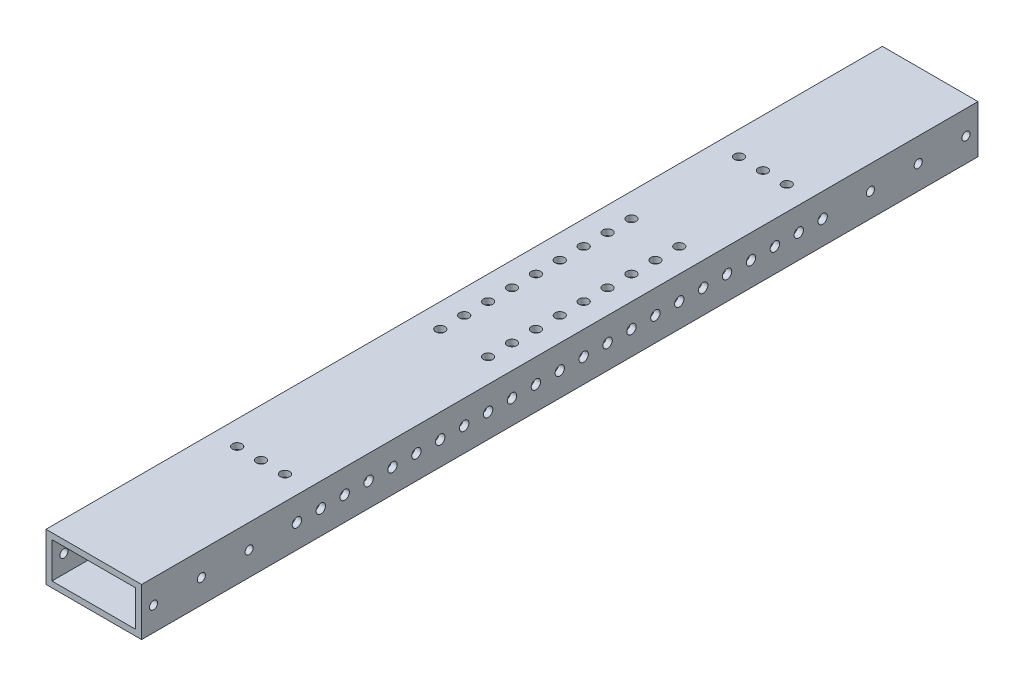
SolidWorks part; units mm, degrees
material "6061-T6 (SS)"
ref_plane "Front Plane" through (0, 0, 0) normal (0, 0, 1) x (1, 0, 0)
ref_plane "Top Plane" through (0, 0, 0) normal (0, 1, 0) x (1, 0, 0)
ref_plane "Right Plane" through (0, 0, 0) normal (1, 0, 0) x (0, 0, -1)
sketch "Sketch1" plane through (0, 0, 0) normal (0, 0, 1) x (1, 0, 0)
  line L0 (-22.225, 9.525) -> (22.225, 9.525)
  line L1 (-25.4, 12.7) -> (25.4, 12.7)
  line L2 (-25.4, 12.7) -> (-25.4, -12.7)
  line L3 (-25.4, -12.7) -> (25.4, -12.7)
  line L4 (25.4, 12.7) -> (25.4, -12.7)
  line L5 (22.225, 9.525) -> (22.225, -9.525)
  line L6 (-22.225, -9.525) -> (22.225, -9.525)
  line L7 (-22.225, 9.525) -> (-22.225, -9.525)
  line L8 (-25.4, 12.7) -> (25.4, -12.7) construction
  line L9 (25.4, 12.7) -> (-25.4, -12.7) construction
  point P5 (0, 0)
  dimension "D1" = 50.8
  dimension "D2" = 25.4
  dimension "D3" = 3.175
extrude "Boss-Extrude1" add sketch "Sketch1" along normal mid plane 444.5
sketch "Sketch3" plane through (25.4, 0, 0) normal (1, 0, 0) x (0, 0, -1)
  line L0 (-222.25, -12.7) -> (-222.25, 12.7) construction
  line L1 (-222.25, 12.7) -> (222.25, 12.7) construction
  line L2 (222.25, -12.7) -> (222.25, 12.7) construction
  circle A0 centre (-215.9, 0) radius 2.1527
  circle A1 centre (-190.5, 0) radius 2.1527
  circle A2 centre (-165.1, 0) radius 2.1527
  circle A3 centre (215.9, 0) radius 2.159
  circle A4 centre (190.5, 0) radius 2.159
  circle A5 centre (165.1, 0) radius 2.159
  dimension "D2" = 4.3053
  dimension "D9" = 4.318
  dimension "D1" = 6.35
  dimension "D3" = 12.7
  dimension "D4" = 31.75
  dimension "D5" = 12.7
  dimension "D6" = 57.15
  dimension "D7" = 12.7
  dimension "D8" = 6.35
  dimension "D10" = 12.7
  dimension "D11" = 31.75
  dimension "D12" = 57.15
  dimension "D13" = 12.7
  dimension "D14" = 12.7
extrude "Cut-Extrude2" cut sketch "Sketch3" against normal through all
sketch "Sketch4" plane through (25.4, 0, 0) normal (1, 0, 0) x (0, 0, -1)
  line L1 (-222.25, -12.7) -> (-222.25, 12.7) construction
  line L2 (-222.25, -12.7) -> (222.25, -12.7) construction
  circle A2 centre (-215.9, 0) radius 2.4892 construction
  circle A3 centre (-203.2, 0) radius 2.4892 construction
  circle A16 centre (-190.5, 0) radius 2.4892 construction
  circle A17 centre (-177.8, 0) radius 2.4892 construction
  circle A18 centre (-165.1, 0) radius 2.4892 construction
  circle A35 centre (-152.4, 0) radius 2.4892
  circle A36 centre (-139.7, 0) radius 2.4892
  circle A37 centre (-127, 0) radius 2.4892
  circle A38 centre (-114.3, 0) radius 2.4892
  circle A39 centre (-101.6, 0) radius 2.4892
  circle A40 centre (-88.9, 0) radius 2.4892
  circle A41 centre (-76.2, 0) radius 2.4892
  circle A42 centre (-63.5, 0) radius 2.4892
  circle A43 centre (-50.8, 0) radius 2.4892
  circle A44 centre (-38.1, 0) radius 2.4892
  circle A45 centre (-25.4, 0) radius 2.4892
  circle A46 centre (-12.7, 0) radius 2.4892
  circle A47 centre (0, 0) radius 2.4892
  circle A48 centre (12.7, 0) radius 2.4892
  circle A49 centre (25.4, 0) radius 2.4892
  circle A50 centre (38.1, 0) radius 2.4892
  circle A51 centre (50.8, 0) radius 2.4892
  circle A52 centre (63.5, 0) radius 2.4892
  circle A53 centre (76.2, 0) radius 2.4892
  circle A54 centre (88.9, 0) radius 2.4892
  circle A55 centre (101.6, 0) radius 2.4892
  circle A56 centre (114.3, 0) radius 2.4892
  circle A57 centre (127, 0) radius 2.4892
  circle A58 centre (139.7, 0) radius 2.4892
  circle A59 centre (152.4, 0) radius 2.4892
  circle A60 centre (165.1, 0) radius 2.4892 construction
  circle A61 centre (177.8, 0) radius 2.4892 construction
  circle A62 centre (190.5, 0) radius 2.4892 construction
  circle A63 centre (203.2, 0) radius 2.4892 construction
  dimension "D2" = 4.9784
  dimension "D1" = 6.35
  dimension "D3" = 12.7
  dimension "D4" = 12.7
  dimension "D5" = 34
extrude "Cut-Extrude3" cut sketch "Sketch4" against normal through all contours A36 | A37 | A38 | A39 | A40 | A41 | A42 | A43 | A44 | A45 | A46 | A47 | A48 | A49 | A50 | A51 | A52 | A53 | A54 | A55 | A56 | A57 | A58
sketch "Sketch5" plane through (0, -12.7, 0) normal (0, -1, 0) x (1, 0, 0)
  line L0 (-25.4, 0) -> (25.4, 0) construction
  line L4 (25.4, 222.25) -> (25.4, -222.25) construction
  line L5 (-25.4, 222.25) -> (-25.4, -222.25) construction
  line L6 (-25.4, 222.25) -> (25.4, 222.25) construction
  circle A0 centre (-12.7, 133.35) radius 2.4892
  circle A1 centre (0, 133.35) radius 2.4892
  circle A2 centre (12.7, 133.35) radius 2.4892
  circle A3 centre (12.7, -133.35) radius 2.4892
  circle A4 centre (0, -133.35) radius 2.4892
  circle A5 centre (-12.7, -133.35) radius 2.4892
  circle A6 centre (-12.7, 25.4) radius 2.4892
  circle A7 centre (0, 25.4) radius 2.4892 construction
  circle A8 centre (12.7, 25.4) radius 2.4892
  circle A9 centre (12.7, 12.7) radius 2.4892
  circle A10 centre (0, 12.7) radius 2.4892 construction
  circle A11 centre (-12.7, 12.7) radius 2.4892
  circle A12 centre (12.7, 0) radius 2.4892
  circle A13 centre (0, 0) radius 2.4892 construction
  circle A14 centre (-12.7, 0) radius 2.4892
  circle A15 centre (12.7, -12.7) radius 2.4892
  circle A16 centre (0, -12.7) radius 2.4892 construction
  circle A17 centre (-12.7, -12.7) radius 2.4892
  circle A18 centre (12.7, -25.4) radius 2.4892
  circle A19 centre (0, -25.4) radius 2.4892 construction
  circle A20 centre (-12.7, -25.4) radius 2.4892
  circle A21 centre (12.7, -38.1) radius 2.4892
  circle A22 centre (0, -38.1) radius 2.4892 construction
  circle A23 centre (-12.7, -38.1) radius 2.4892
  circle A24 centre (12.7, -50.8) radius 2.4892
  circle A25 centre (0, -50.8) radius 2.4892 construction
  circle A26 centre (-12.7, -50.8) radius 2.4892
  circle A27 centre (12.7, -63.5) radius 2.4892
  circle A28 centre (0, -63.5) radius 2.4892 construction
  circle A29 centre (-12.7, -63.5) radius 2.4892
  circle A30 centre (12.7, -76.2) radius 2.4892
  circle A31 centre (0, -76.2) radius 2.4892 construction
  circle A32 centre (-12.7, -76.2) radius 2.4892
  dimension "D1" = 4.9784
  dimension "D3" = 12.7
  dimension "D2" = 88.9
  dimension "D5" = 12.7
  dimension "D4" = 12.7
  dimension "D6" = 107.95
  dimension "D8" = 12.7
  dimension "D7" = 9
extrude "Cut-Extrude4" cut sketch "Sketch5" against normal through all
